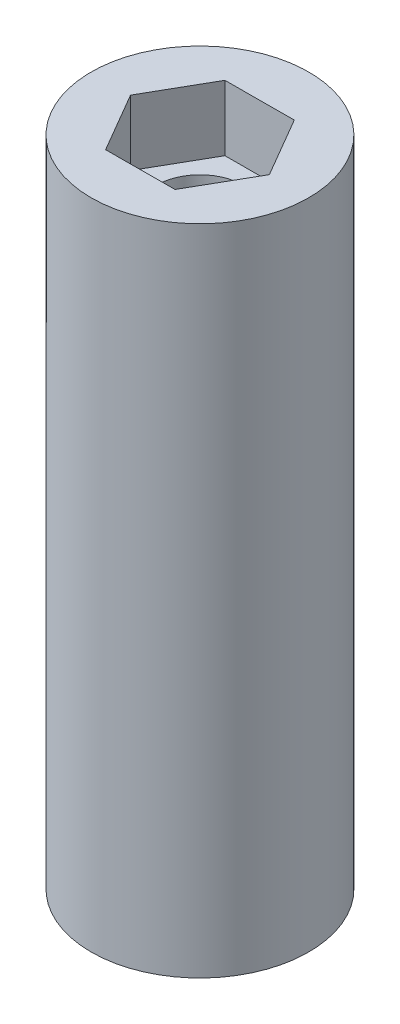
SolidWorks part; units mm, degrees
ref_plane "Front Plane" through (0, 0, 0) normal (0, 0, 1) x (1, 0, 0)
ref_plane "Top Plane" through (0, 0, 0) normal (0, 1, 0) x (1, 0, 0)
ref_plane "Right Plane" through (0, 0, 0) normal (1, 0, 0) x (0, 0, -1)
sketch "Sketch1" plane through (0, 0, 0) normal (0, 1, 0) x (1, 0, 0)
  circle A0 centre (0, 0) radius 5
  dimension "D1" = 10
extrude "Boss-Extrude1" add sketch "Sketch1" along normal blind 30
sketch "Sketch2" plane through (0, 30, 0) normal (0, 1, 0) x (1, 0, 0)
  circle A0 centre (0, 0) radius 2
  dimension "D1" = 4
extrude "Cut-Extrude1" cut sketch "Sketch2" against normal through all
sketch "Sketch3" plane through (0, 30, 0) normal (0, 1, 0) x (1, 0, 0)
  line L1 (1.599, -2.7434) -> (3.1754, 0.0131)
  line L2 (3.1754, 0.0131) -> (1.5764, 2.7565)
  line L3 (1.5764, 2.7565) -> (-1.599, 2.7434)
  line L4 (-1.599, 2.7434) -> (-3.1754, -0.0131)
  line L5 (-3.1754, -0.0131) -> (-1.5764, -2.7565)
  line L6 (-1.5764, -2.7565) -> (1.599, -2.7434)
  circle A0 centre (0, 0) radius 2.75 construction
  dimension "D1" = 5.5
extrude "Cut-Extrude2" cut sketch "Sketch3" against normal blind 3
pattern_linear "LPattern1" count 2 spacing 27 along (0, -1, 0) of "Cut-Extrude2"
